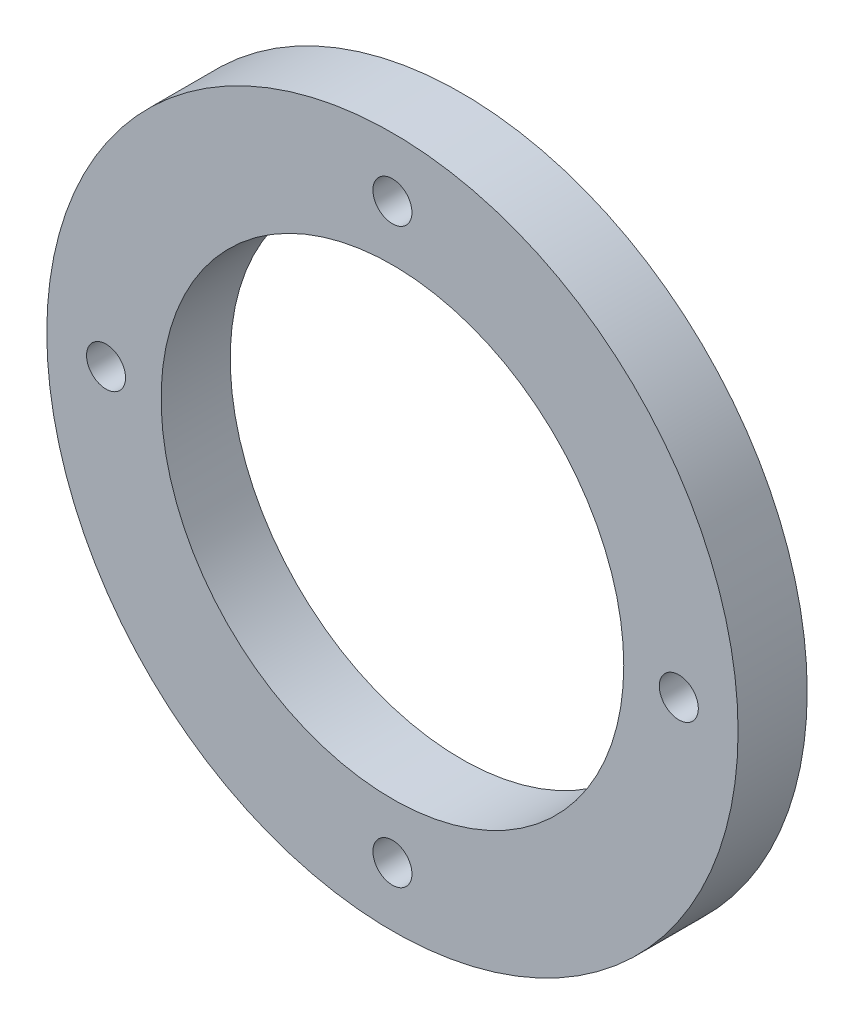
SolidWorks part; units mm, degrees
ref_plane "Front Plane" through (0, 0, 0) normal (0, 0, 1) x (1, 0, 0)
ref_plane "Top Plane" through (0, 0, 0) normal (0, 1, 0) x (1, 0, 0)
ref_plane "Right Plane" through (0, 0, 0) normal (1, 0, 0) x (0, 0, -1)
sketch "Sketch1" plane through (0, 0, 0) normal (0, 0, 1) x (1, 0, 0)
  circle A0 centre (0, 0) radius 35
  circle A1 centre (0, 0) radius 23.425
  circle A2 centre (0, 29) radius 1.975
  circle A3 centre (29, 0) radius 1.975
  circle A4 centre (0, -29) radius 1.975
  circle A5 centre (-29, 0) radius 1.975
  point P15 (0, 0)
  dimension "D1" = 70
  dimension "D2" = 46.85
  dimension "D3" = 3.95
  dimension "D4" = 29
  dimension "D5" = 4
extrude "Boss-Extrude1" add sketch "Sketch1" along normal blind 5
sketch "Sketch4" plane through (0, 0, 5) normal (0, 0, 1) x (1, 0, 0)
  circle A0 centre (0, 0) radius 35
  circle A1 centre (0, 0) radius 23.425
  circle A2 centre (0, 29) radius 1.975
  circle A3 centre (29, 0) radius 1.975
  circle A4 centre (0, -29) radius 1.975
  circle A5 centre (-29, 0) radius 1.975
  point P16 (0, 0)
  dimension "D1" = 4
extrude "Boss-Extrude3" add sketch "Sketch4" along normal blind 2
